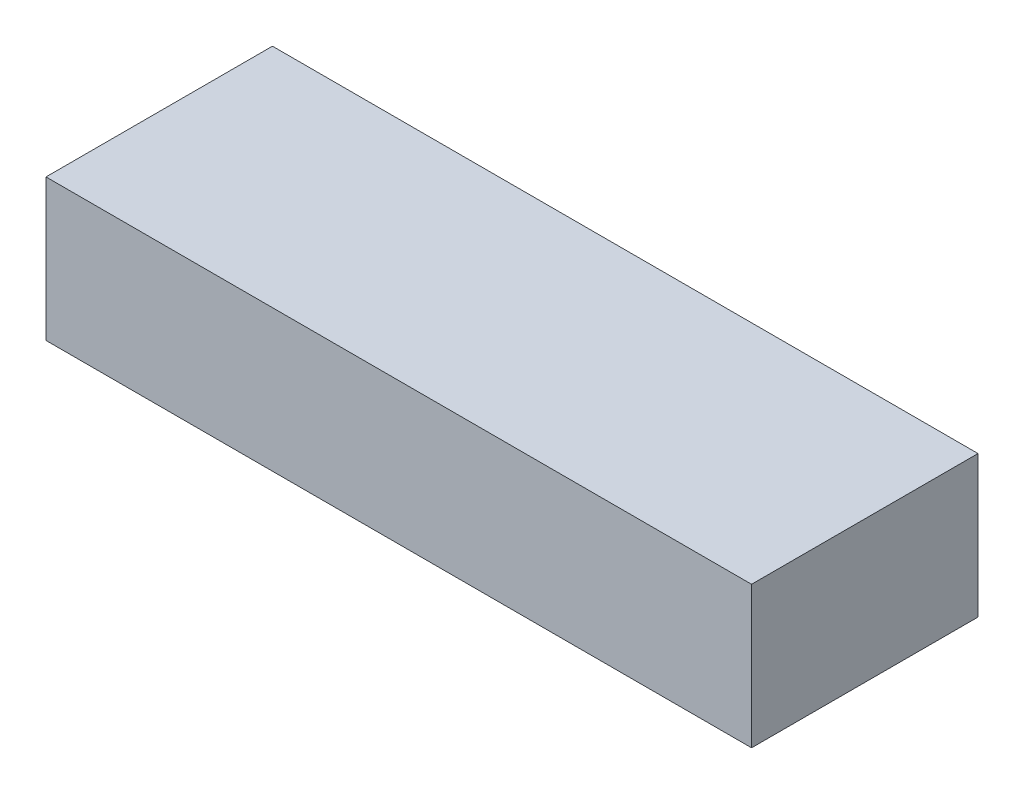
SolidWorks part; units mm, degrees
ref_plane "Front Plane" through (0, 0, 0) normal (0, 0, 1) x (1, 0, 0)
ref_plane "Top Plane" through (0, 0, 0) normal (0, 1, 0) x (1, 0, 0)
ref_plane "Right Plane" through (0, 0, 0) normal (1, 0, 0) x (0, 0, -1)
sketch "Sketch1" plane through (0, 0, 0) normal (0, 1, 0) x (1, 0, 0)
  line L1 (-34.6752, 9.7242) -> (72.1648, 9.7242)
  line L2 (-34.6752, 9.7242) -> (-34.6752, -24.5658)
  line L3 (-34.6752, -24.5658) -> (72.1648, -24.5658)
  line L4 (72.1648, 9.7242) -> (72.1648, -24.5658)
  dimension "D1" = 34.29
  dimension "D2" = 106.84
extrude "Boss-Extrude1" add sketch "Sketch1" along normal blind 21.45
